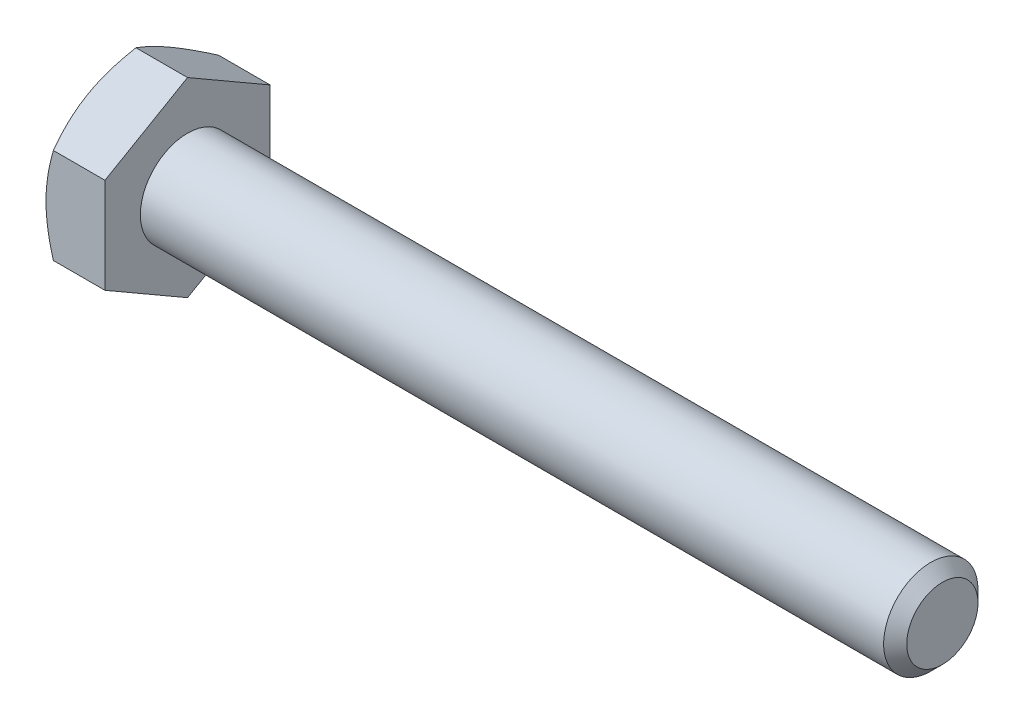
SolidWorks part; units mm, degrees
material "Alloy Steel"
ref_plane "Front Plane" through (0, 0, 0) normal (0, 0, 1) x (1, 0, 0)
ref_plane "Top Plane" through (0, 0, 0) normal (0, 1, 0) x (1, 0, 0)
ref_plane "Right Plane" through (0, 0, 0) normal (1, 0, 0) x (0, 0, -1)
sketch "Sketch1" plane through (0, 0, 0) normal (0, 0, 1) x (1, 0, 0)
  line L0 (-27.3844, 0) -> (27.3844, 0) construction
  line L1 (27.3844, 3.175) -> (27.3844, -3.175) construction
  line L2 (-23.4156, 5.5562) -> (-23.4156, -5.5562) construction
  line L3 (-27.3844, 5.5562) -> (-27.3844, -5.5562) construction
  point P9 (-23.4156, 0)
  point P10 (22.9394, -3.175)
  dimension "D1" = 4.445
  dimension "Screw Dia" = 6.35
  dimension "Hex" = 11.1125
  dimension "Head Ht" = 3.9688
  dimension "Screw Lenght" = 50.8
ref_plane "Plane2" through (27.3844, 0, 0) normal (1, 0, 0) x (0, 0, -1)
sketch "Sketch5" plane through (27.3844, 0, 0) normal (1, 0, 0) x (0, 0, -1)
  circle A0 centre (0, 0) radius 3.175
extrude "Boss-Extrude3" add sketch "Sketch5" against normal up to vertex (50.8 mm away) up to point (-23.4156, 0, 0)
sketch "Sketch9" plane through (27.3844, 0, 0) normal (1, 0, 0) x (0, 0, -1)
  circle A1 centre (0, 0) radius 3.175
  circle A2 centre (0, 0) radius 3.175
  dimension "D1" = 0
curve "Helix/Spiral1" pitch 1.27 height 52.07 turns 41 parameters "Pitch"=1.27
chamfer "Chamfer1" distance 0.7772 angle 45 1 edges at (27.3844, 0, -3.175)
sketch "Sketch10" plane through (0, 0, 0) normal (0, 0, 1) x (1, 0, 0)
  line L0 (27.3844, 3.175) -> (27.8606, 2.3501)
  line L1 (27.8606, 2.3501) -> (28.0194, 2.3501)
  line L2 (28.0194, 2.3501) -> (28.4956, 3.175)
  line L3 (27.3844, 3.175) -> (28.4956, 3.175)
  line L4 (27.94, 3.175) -> (27.94, 2.3501) construction
  line L5 (27.6225, 2.7626) -> (28.2575, 2.7626) construction
  dimension "D1" = 60
  dimension "D2" = 0.1588
  dimension "D3" = 0.635
sketch "Sketch6" plane through (-23.4156, 0, 0) normal (-1, 0, 0) x (0, 0, 1)
  line L0 (0, 5.5562) -> (0, -5.5562) construction
  line L1 (5.5563, 3.2079) -> (0, 6.4158)
  line L2 (0, 6.4158) -> (-5.5562, 3.2079)
  line L3 (-5.5562, 3.2079) -> (-5.5562, -3.2079)
  line L4 (-5.5562, -3.2079) -> (0, -6.4158)
  line L5 (0, -6.4158) -> (5.5563, -3.2079)
  line L6 (5.5563, -3.2079) -> (5.5563, 3.2079)
  circle A0 centre (0, 0) radius 5.5563 construction
extrude "Boss-Extrude4" add sketch "Sketch6" along normal up to vertex (3.9688 mm away) up to point (-27.3844, -5.5562, 0)
sketch "Sketch7" plane through (-27.3844, 0, 0) normal (-1, 0, 0) x (0, 0, 1)
  circle A0 centre (0, 0) radius 5.5563 construction
  circle A1 centre (0, 0) radius 5.5563
sketch "Sketch8" plane through (-27.3844, 0, 0) normal (-1, 0, 0) x (0, 0, 1)
  circle A0 centre (0, 0) radius 5.5563 construction
  circle A1 centre (0, 0) radius 5.5563
extrude "Cut-Extrude3" cut sketch "Sketch8" against normal through all draft 60 flip side to cut
sketch "Sketch12" plane through (-27.3844, 0, 0) normal (-1, 0, 0) x (0, 0, 1)
  line L0 (0, 4.2783) -> (0, 2.3892) construction
  line L1 (0.1667, 4.2783) -> (0.1667, 2.3892)
  line L2 (-0.1667, 4.2783) -> (-0.1667, 2.3892)
  line L3 (0, 3.175) -> (0, -3.175) construction
  arc A0 (0.1667, 4.2783) -> (-0.1667, 4.2783) centre (0, 4.2783) ccw
  arc A1 (-0.1667, 2.3892) -> (0.1667, 2.3892) centre (0, 2.3892) ccw
  circle A3 centre (0, 0) radius 2.2225 construction
  circle A4 centre (0, 0) radius 4.445 construction
  point P2 (0, 3.3337)
  dimension "D1" = 4.445
  dimension "D3" = 8.89
  dimension "D2" = 0.3334
extrude "Cut-Extrude4" cut sketch "Sketch12" against normal blind 0.254
pattern_circular "CirPattern1" count 3 over 360 about axis through (0, 0, 0) along (1, 0, 0) of "Cut-Extrude4"
equation "\"D2@Sketch10\" = \"Pitch@Helix/Spiral1\"*.125"
equation "\"D3@Sketch10\" = \"Pitch@Helix/Spiral1\"*.5"
equation "\"D1@Chamfer1\" = \"Pitch@Helix/Spiral1\"*.612"
equation "\"D1@Sketch12\" = \"Hex@Sketch1\"*.4"
equation "\"D3@Sketch12\" = \"Hex@Sketch1\"*.8"
equation "\"D2@Sketch12\" = \"Hex@Sketch1\"*.03"
equation "\"D1@Sketch1\" = \"Pitch@Helix/Spiral1\"*3.5"
equation "\"D3@Helix/Spiral1\" = \"Screw Lenght@Sketch1\"+\"Pitch@Helix/Spiral1\""
